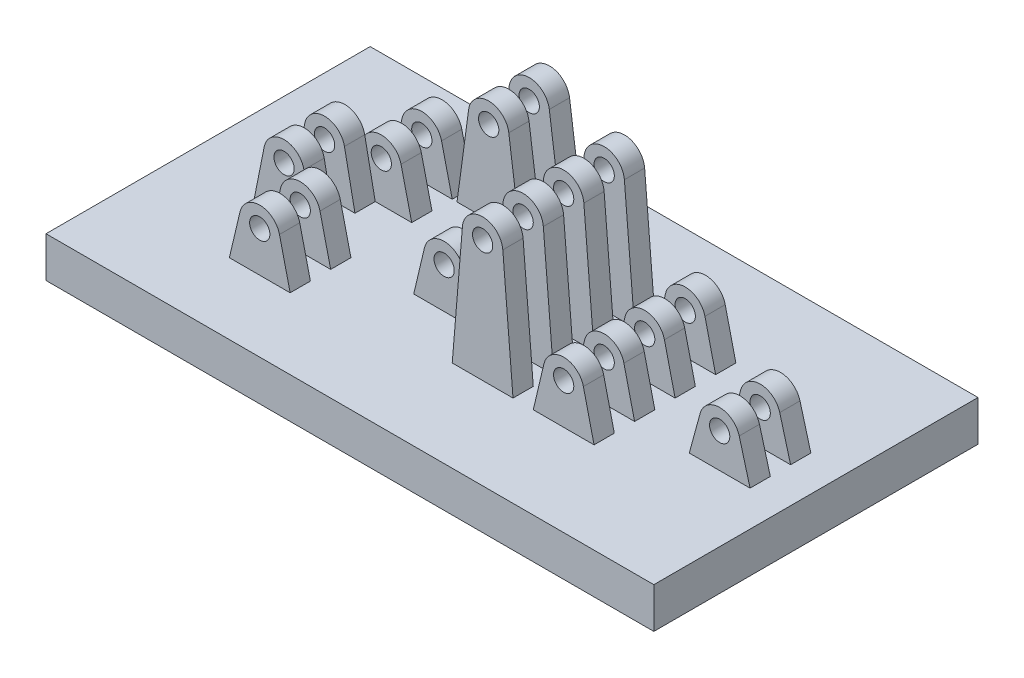
SolidWorks part; units mm, degrees
ref_plane "前基準面" through (0, 0, 0) normal (0, 0, 1) x (1, 0, 0)
ref_plane "上基準面" through (0, 0, 0) normal (0, 1, 0) x (1, 0, 0)
ref_plane "右基準面" through (0, 0, 0) normal (1, 0, 0) x (0, 0, -1)
sketch "草圖1" plane through (0, 0, 0) normal (0, 0, 1) x (1, 0, 0)
  circle A0 centre (-15.5, 2) radius 2.5
  circle A1 centre (-6.5, 0) radius 2.5
  circle A2 centre (10, 10.5) radius 2.5
  circle A3 centre (24, 0) radius 2.5
  circle A4 centre (43.5, 20) radius 2.5
  circle A5 centre (63.5, 0) radius 2.5
  circle A6 centre (92, -1.5) radius 2.5
  point P14 (0, 0)
  point P16 (71.2303, -5.8502)
  dimension "D1" = 5
  dimension "D7" = 6.5
  dimension "D2" = 2
  dimension "D3" = 10.5
  dimension "D4" = 20
  dimension "D5" = 1.5
  dimension "D6" = 15.5
  dimension "D8" = 10
  dimension "D9" = 24
  dimension "D10" = 43.5
  dimension "D11" = 63.5
  dimension "D12" = 92
sketch "草圖3" plane through (0, 0, 0) normal (0, 1, 0) x (1, 0, 0)
  line L0 (-41.75, 0) -> (0, 0) construction
  line L1 (-41.75, 40) -> (108.25, 40)
  line L2 (-41.75, 40) -> (-41.75, -40)
  line L3 (-41.75, -40) -> (108.25, -40)
  line L4 (108.25, 40) -> (108.25, -40)
  line L5 (92, 0) -> (-15.5, 0) construction
  line L6 (38.25, 0) -> (38.25, 40) construction
  line L7 (33.25, 40) -> (33.25, 19.5022) construction
  dimension "D1" = 150
  dimension "D2" = 80
  dimension "D3" = 5
extrude "填料-伸長3" add sketch "草圖3" against normal blind 10 from offset 10 offset against normal yes
sketch "草圖5" plane through (0, 0, 0) normal (0, 0, 1) x (1, 0, 0)
  line L0 (-11.3661, 1.1495) -> (-14, -10)
  line L1 (-41.75, -10) -> (108.25, -10) construction
  line L2 (-14, -10) -> (1, -10)
  line L3 (-6.5, -10) -> (-6.5, 0) construction
  line L4 (-1.6339, 1.1495) -> (1, -10)
  circle A0 centre (-6.5, 0) radius 2.5 construction
  circle A1 centre (-6.5, 0) radius 2.5
  arc A2 (-1.6339, 1.1495) -> (-11.3661, 1.1495) centre (-6.5, 0) ccw
  circle A3 centre (-6.5, 0) radius 5 construction
  dimension "D2" = 15
  dimension "D1" = 2.5
extrude "填料-伸長5" add sketch "草圖5" along normal mid plane 45
sketch "草圖6" plane through (0, -10, 0) normal (0, 1, 0) x (1, 0, 0)
  line L0 (-11.3661, -22.5) -> (-1.6339, -22.5) construction
  line L1 (-29.2714, 7.5) -> (24.2931, 7.5)
  line L2 (-29.2714, 7.5) -> (-29.2714, -7.5)
  line L3 (-29.2714, -7.5) -> (24.2931, -7.5)
  line L4 (24.2931, 7.5) -> (24.2931, -7.5)
  line L5 (-31.9055, -12.5) -> (23.4108, -12.5)
  line L6 (-31.9055, -12.5) -> (-31.9055, -17.5)
  line L7 (-31.9055, -17.5) -> (23.4108, -17.5)
  line L8 (23.4108, -12.5) -> (23.4108, -17.5)
  line L9 (-26.6373, 17.5) -> (23.4108, 17.5)
  line L10 (-26.6373, 17.5) -> (-26.6373, 12.5)
  line L11 (-26.6373, 12.5) -> (23.4108, 12.5)
  line L12 (23.4108, 17.5) -> (23.4108, 12.5)
  line L13 (-1.6339, 22.5) -> (-11.3661, 22.5) construction
  line L14 (-29.2714, 0) -> (0, 0) construction
  dimension "D1" = 5
  dimension "D2" = 5
  dimension "D3" = 5
  dimension "D4" = 5
  dimension "D5" = 15
extrude "除料-伸長1" cut sketch "草圖6" along normal blind 40
sketch "草圖7" plane through (0, 0, 0) normal (0, 0, 1) x (1, 0, 0)
  line L0 (58.6339, 1.1495) -> (56, -10)
  line L1 (-41.75, -10) -> (108.25, -10) construction
  line L2 (56, -10) -> (71, -10)
  line L3 (63.5, -10) -> (63.5, 0) construction
  line L4 (68.3661, 1.1495) -> (71, -10)
  line L5 (38.517, 20.4124) -> (36, -10)
  line L6 (36, -10) -> (51, -10)
  line L7 (43.5, -10) -> (43.5, 20) construction
  line L8 (48.483, 20.4124) -> (51, -10)
  circle A0 centre (63.5, 0) radius 2.5 construction
  circle A1 centre (63.5, 0) radius 2.5
  arc A2 (68.3661, 1.1495) -> (58.6339, 1.1495) centre (63.5, 0) ccw
  circle A3 centre (63.5, 0) radius 5 construction
  circle A4 centre (43.5, 20) radius 2.5 construction
  circle A5 centre (43.5, 20) radius 2.5
  arc A6 (48.483, 20.4124) -> (38.517, 20.4124) centre (43.5, 20) ccw
  circle A7 centre (43.5, 20) radius 5 construction
  dimension "D2" = 15
  dimension "D4" = 15
  dimension "D1" = 2.5
  dimension "D3" = 2.5
extrude "填料-伸長6" add sketch "草圖7" along normal mid plane 35
sketch "草圖4" plane through (0, 0, 0) normal (0, 0, 1) x (1, 0, 0)
  line L0 (87.1761, -0.1848) -> (84.5, -10)
  line L1 (-41.75, -10) -> (108.25, -10) construction
  line L2 (84.5, -10) -> (99.5, -10)
  line L3 (92, -10) -> (92, -1.5) construction
  line L4 (96.8239, -0.1848) -> (99.5, -10)
  line L5 (-20.4028, 2.9809) -> (-23, -10)
  line L6 (-23, -10) -> (-8, -10)
  line L7 (-15.5, -10) -> (-15.5, 2) construction
  line L8 (19.1339, 1.1495) -> (16.5, -10)
  line L9 (16.5, -10) -> (31.5, -10)
  line L10 (24, -10) -> (24, 0) construction
  line L11 (-10.5972, 2.9809) -> (-8, -10)
  line L12 (28.8661, 1.1495) -> (31.5, -10)
  line L13 (38.517, 20.4124) -> (36, -10) construction
  line L14 (36, -10) -> (51, -10) construction
  line L15 (43.5, -10) -> (43.5, 20) construction
  line L16 (48.483, 20.4124) -> (51, -10) construction
  circle A0 centre (92, -1.5) radius 2.5 construction
  circle A1 centre (24, 0) radius 2.5 construction
  circle A2 centre (-15.5, 2) radius 2.5 construction
  circle A3 centre (92, -1.5) radius 2.5
  circle A4 centre (24, 0) radius 2.5
  circle A5 centre (-15.5, 2) radius 2.5
  arc A6 (96.8239, -0.1848) -> (87.1761, -0.1848) centre (92, -1.5) ccw
  arc A7 (28.8661, 1.1495) -> (19.1339, 1.1495) centre (24, 0) ccw
  arc A8 (-10.5972, 2.9809) -> (-20.4028, 2.9809) centre (-15.5, 2) ccw
  circle A9 centre (92, -1.5) radius 5 construction
  circle A10 centre (24, 0) radius 5 construction
  circle A11 centre (-15.5, 2) radius 5 construction
  circle A12 centre (43.5, 20) radius 2.5 construction
  circle A13 centre (43.5, 20) radius 2.5 construction
  arc A14 (48.483, 20.4124) -> (38.517, 20.4124) centre (43.5, 20) ccw construction
  circle A15 centre (43.5, 20) radius 5 construction
  dimension "D2" = 15
  dimension "D3" = 15
  dimension "D4" = 15
  dimension "D6" = 15
  dimension "D1" = 2.5
  dimension "D5" = 2.5
extrude "填料-伸長4" add sketch "草圖4" along normal mid plane 15
sketch "草圖9" plane through (0, 0, 0) normal (0, 0, 1) x (1, 0, 0)
  line L0 (5.0451, 11.1699) -> (2.183, -10)
  line L1 (-41.75, -10) -> (108.25, -10) construction
  line L2 (2.183, -10) -> (17.817, -10)
  line L3 (10, -10) -> (10, 10.5) construction
  line L4 (14.9549, 11.1699) -> (17.817, -10)
  circle A0 centre (10, 10.5) radius 2.5 construction
  circle A1 centre (10, 10.5) radius 2.5
  arc A2 (14.9549, 11.1699) -> (5.0451, 11.1699) centre (10, 10.5) ccw
  circle A3 centre (10, 10.5) radius 5 construction
  dimension "D1" = 2.5
extrude "填料-伸長7" add sketch "草圖9" against normal blind 15 from offset 17.5 offset against normal yes
sketch "草圖8" plane through (0, -10, 0) normal (0, 1, 0) x (1, 0, 0)
  line L0 (-36.5539, 0) -> (0, 0) construction
  line L1 (-36.5539, 2.5) -> (113.2805, 2.5)
  line L2 (-36.5539, 2.5) -> (-36.5539, -2.5)
  line L3 (-36.5539, -2.5) -> (113.2805, -2.5)
  line L4 (113.2805, 2.5) -> (113.2805, -2.5)
  line L6 (34.2477, 12.5) -> (87.7141, 12.5)
  line L7 (34.2477, 12.5) -> (34.2477, 7.5)
  line L8 (34.2477, 7.5) -> (87.7141, 7.5)
  line L9 (87.7141, 12.5) -> (87.7141, 7.5)
  line L11 (33.6373, -7.5) -> (80.1217, -7.5)
  line L12 (33.6373, -7.5) -> (33.6373, -12.5)
  line L13 (33.6373, -12.5) -> (80.1217, -12.5)
  line L14 (80.1217, -7.5) -> (80.1217, -12.5)
  line L15 (71, 17.5) -> (68.3661, 17.5) construction
  line L16 (2.183, 32.5) -> (17.817, 32.5) construction
  line L17 (23.5295, 27.5) -> (1.5589, 27.5)
  line L18 (23.5295, 27.5) -> (23.5295, 22.5)
  line L19 (23.5295, 22.5) -> (1.5589, 22.5)
  line L20 (1.5589, 27.5) -> (1.5589, 22.5)
  point P20 (69.683, 17.5)
  dimension "D1" = 5
  dimension "D2" = 5
  dimension "D3" = 5
  dimension "D4" = 5
  dimension "D5" = 5
  dimension "D6" = 5
  dimension "D7" = 5
extrude "除料-伸長2" cut sketch "草圖8" along normal blind 35
sketch "草圖2" plane through (0, 0, 0) normal (0, 0, 1) x (1, 0, 0)
  line L0 (-24.4563, -20) -> (0.5437, -20)
  line L1 (96.8815, -0.4178) -> (101.2227, -20)
  line L2 (87.1185, -0.4178) -> (82.7773, -20)
  line L3 (92, -1.5) -> (92, -20) construction
  line L4 (68.3815, 1.0822) -> (73.0553, -20)
  line L5 (58.6185, 1.0822) -> (53.9447, -20)
  line L6 (48.481, 20.4358) -> (52.0186, -20)
  line L7 (38.519, 20.4358) -> (34.9814, -20)
  line L8 (19.019, 0.4358) -> (17.2311, -20)
  line L9 (28.981, 0.4358) -> (30.7689, -20)
  line L10 (5.0122, 10.8488) -> (2.855, -20)
  line L11 (14.9878, 10.8488) -> (17.145, -20)
  line L12 (63.5, 0) -> (63.5, -20) construction
  line L13 (43.5, 20) -> (43.5, -20) construction
  line L14 (24, 0) -> (24, -20) construction
  line L15 (10, 10.5) -> (10, -20) construction
  line L16 (-6.5, 0) -> (-6.5, -20) construction
  line L17 (-15.5, 2) -> (-15.5, -20) construction
  line L18 (-1.5253, 0.502) -> (0.5437, -20)
  line L19 (-20.424, 2.8682) -> (-24.4563, -20)
  line L20 (82.7773, -20) -> (101.2227, -20)
  line L21 (53.9447, -20) -> (73.0553, -20)
  line L22 (34.9814, -20) -> (52.0186, -20)
  line L23 (17.2311, -20) -> (30.7689, -20)
  line L24 (2.855, -20) -> (17.145, -20)
  circle A0 centre (-15.5, 2) radius 2.5 construction
  circle A1 centre (-6.5, 0) radius 2.5 construction
  circle A2 centre (10, 10.5) radius 2.5 construction
  circle A3 centre (24, 0) radius 2.5 construction
  circle A4 centre (43.5, 20) radius 2.5 construction
  circle A5 centre (63.5, 0) radius 2.5 construction
  circle A6 centre (92, -1.5) radius 2.5 construction
  circle A7 centre (-15.5, 2) radius 2.5
  circle A8 centre (-6.5, 0) radius 2.5
  circle A9 centre (10, 10.5) radius 2.5
  circle A10 centre (24, 0) radius 2.5
  circle A11 centre (43.5, 20) radius 2.5
  circle A12 centre (63.5, 0) radius 2.5
  circle A13 centre (92, -1.5) radius 2.5
  arc A14 (-10.5799, 2.8904) -> (-20.424, 2.8682) centre (-15.5, 2) ccw
  arc A16 (14.9878, 10.8488) -> (5.0122, 10.8488) centre (10, 10.5) ccw
  arc A17 (28.981, 0.4358) -> (19.019, 0.4358) centre (24, 0) ccw
  arc A18 (48.481, 20.4358) -> (38.519, 20.4358) centre (43.5, 20) ccw
  arc A19 (68.3815, 1.0822) -> (58.6185, 1.0822) centre (63.5, 0) ccw
  arc A20 (96.8815, -0.4178) -> (87.1185, -0.4178) centre (92, -1.5) ccw
  circle A21 centre (92, -1.5) radius 5 construction
  circle A22 centre (63.5, 0) radius 5 construction
  circle A23 centre (43.5, 20) radius 5 construction
  circle A24 centre (24, 0) radius 5 construction
  circle A25 centre (10, 10.5) radius 5 construction
  circle A26 centre (-15.5, 2) radius 5 construction
  arc A28 (-1.5253, 0.502) -> (-10.5799, 2.8904) centre (-6.5, 0) ccw
  dimension "D9" = 2.5
  dimension "D2" = 20
  dimension "D3" = 25
  dimension "D4" = 25
  dimension "D5" = 10
  dimension "D6" = 10
  dimension "D7" = 8
  dimension "D8" = 25
  dimension "D10" = 10
  dimension "D1" = 2.5
extrude "填料-伸長1" [suppressed] add sketch "草圖2" along normal mid plane 5
